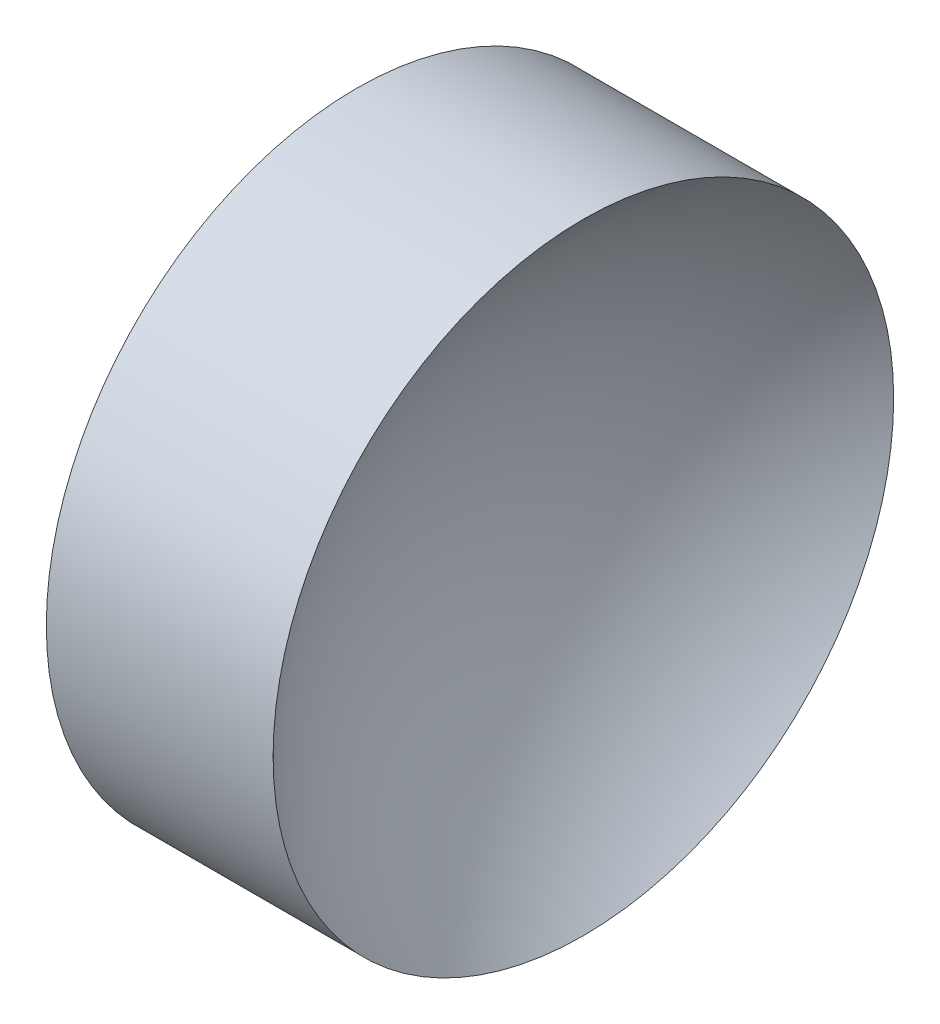
SolidWorks part; units mm, degrees
ref_plane "前视基准面" through (0, 0, 0) normal (0, 0, 1) x (1, 0, 0)
ref_plane "上视基准面" through (0, 0, 0) normal (0, 1, 0) x (1, 0, 0)
ref_plane "右视基准面" through (0, 0, 0) normal (1, 0, 0) x (0, 0, -1)
sketch "草图1" plane through (0, 0, 0) normal (0, 0, 1) x (1, 0, 0)
  line L0 (39.7365, 26.0623) -> (48.2578, 26.0623) construction
  line L1 (41.3658, 26.0623) -> (41.3658, 31.0623)
  line L2 (42.8658, 26.0623) -> (41.3658, 26.0623)
  line L3 (41.3658, 31.0623) -> (45.0199, 31.0623)
  arc A0 (45.0199, 31.0623) -> (42.8658, 26.0623) centre (49.7458, 26.0623) ccw
revolve "旋转1" add sketch "草图1" angle 360 about L0
